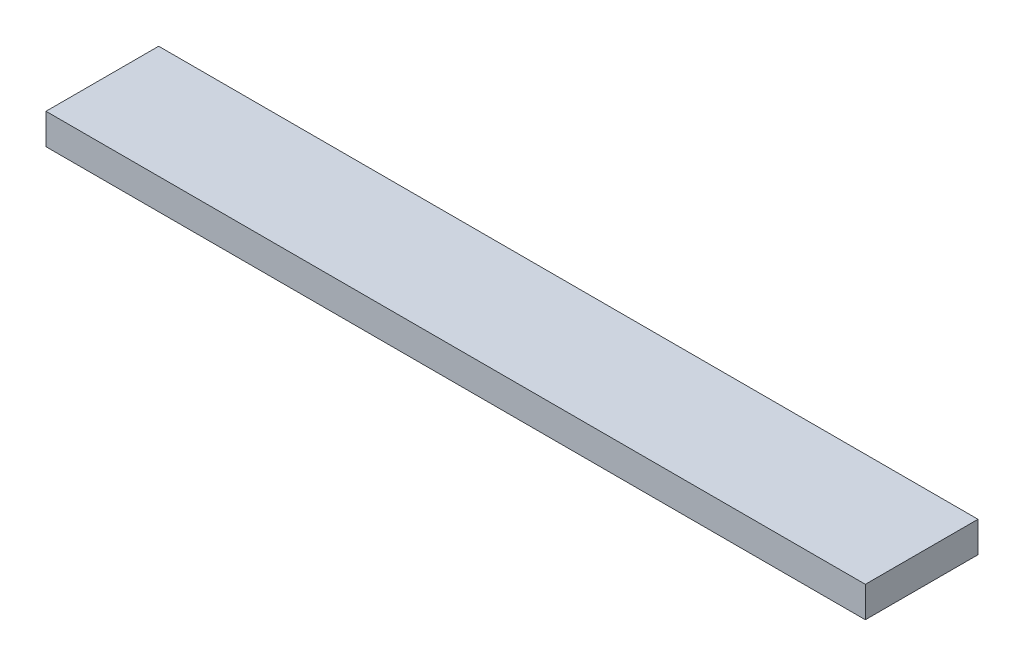
SolidWorks part; units mm, degrees
material "Pine"
ref_plane "Front Plane" through (0, 0, 0) normal (0, 0, 1) x (1, 0, 0)
ref_plane "Top Plane" through (0, 0, 0) normal (0, 1, 0) x (1, 0, 0)
ref_plane "Right Plane" through (0, 0, 0) normal (1, 0, 0) x (0, 0, -1)
sketch "Sketch1" plane through (0, 0, 0) normal (0, 1, 0) x (1, 0, 0)
  line L1 (0, 0) -> (508, 0)
  line L2 (0, 0) -> (0, 69.85)
  line L3 (0, 69.85) -> (508, 69.85)
  line L4 (508, 0) -> (508, 69.85)
  dimension "D1" = 69.85
  dimension "D2" = 508
extrude "Boss-Extrude1" add sketch "Sketch1" along normal blind 19.05
